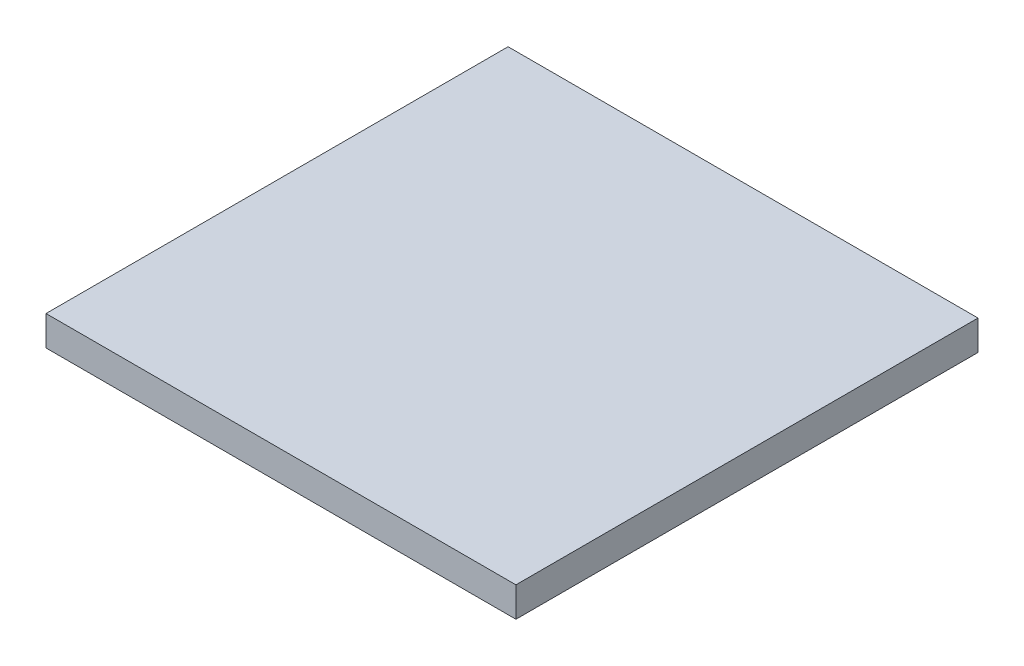
SolidWorks part; units mm, degrees
ref_plane "Front Plane" through (0, 0, 0) normal (0, 0, 1) x (1, 0, 0)
ref_plane "Top Plane" through (0, 0, 0) normal (0, 1, 0) x (1, 0, 0)
ref_plane "Right Plane" through (0, 0, 0) normal (1, 0, 0) x (0, 0, -1)
sketch "Sketch1" plane through (0, 0, 0) normal (0, 1, 0) x (1, 0, 0)
  line L1 (-300, 295) -> (300, 295)
  line L2 (-300, 295) -> (-300, -295)
  line L3 (-300, -295) -> (300, -295)
  line L4 (300, 295) -> (300, -295)
  line L5 (-300, 295) -> (300, -295) construction
  line L6 (-300, -295) -> (300, 295) construction
  point P0 (0, 0)
  dimension "D1" = 600
  dimension "D2" = 590
extrude "Boss-Extrude1" add sketch "Sketch1" along normal blind 38.1
